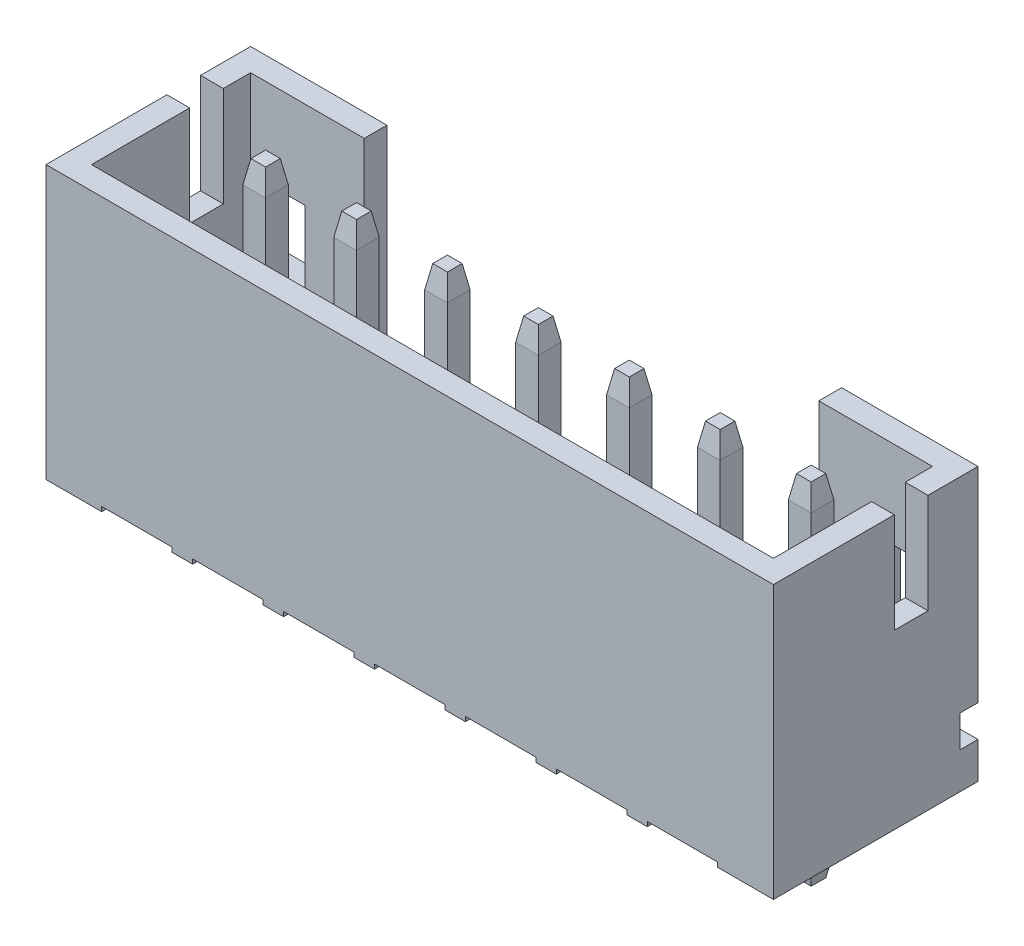
SolidWorks part; units mm, degrees
ref_plane "Front Plane" through (0, 0, 0) normal (0, 0, 1) x (1, 0, 0)
ref_plane "Top Plane" through (0, 0, 0) normal (0, 1, 0) x (1, 0, 0)
ref_plane "Right Plane" through (0, 0, 0) normal (1, 0, 0) x (0, 0, -1)
sketch "Sketch1" plane through (0, 0, 0) normal (0, 1, 0) x (1, 0, 0)
  line L1 (-10, 2.25) -> (6, 2.25)
  line L2 (-10, 2.25) -> (-10, -2.25)
  line L3 (-10, -2.25) -> (6, -2.25)
  line L4 (6, 2.25) -> (6, -2.25)
  dimension "D1" = 16
  dimension "D2" = 4.5
  dimension "D3" = 2.25
  dimension "D4" = 6
extrude "Extrude1" add sketch "Sketch1" along normal blind 6
sketch "Sketch2" plane through (0, 0, 2.25) normal (0, 0, 1) x (1, 0, 0)
  line L0 (-10, 0) -> (6, 0) construction
  line L6 (-0.775, 0.1) -> (0.775, 0.1)
  line L7 (-0.775, 0.1) -> (-0.775, 0)
  line L8 (-0.775, 0) -> (0, 0)
  line L9 (0.775, 0.1) -> (0.775, 0)
  line L10 (0, 0) -> (0.775, 0)
  dimension "D1" = 0.1
  dimension "D3" = 1.55
extrude "Cut-Extrude1" cut sketch "Sketch2" against normal through all
sketch "Sketch3" plane through (0, 6, 0) normal (0, 1, 0) x (-1, 0, 0)
  line L0 (-6, -2.25) -> (10, -2.25) construction
  line L1 (9.5, -1.75) -> (-5.5, -1.75)
  line L2 (9.5, -1.75) -> (9.5, 1.75)
  line L3 (9.5, 1.75) -> (-5.5, 1.75)
  line L4 (-5.5, -1.75) -> (-5.5, 1.75)
  line L5 (10, 2.25) -> (-6, 2.25) construction
  line L6 (-6, 2.25) -> (-6, -2.25) construction
  line L7 (10, -2.25) -> (10, 2.25) construction
  dimension "D1" = 0.5
  dimension "D2" = 0.5
  dimension "D3" = 0.5
  dimension "D4" = 0.5
extrude "Cut-Extrude2" cut sketch "Sketch3" against normal offset from surface (4.2 mm away) 1.8 up to face at (3.3875, 0, 0)
sketch "Sketch5" plane through (-10, 0, 0) normal (-1, 0, 0) x (0, 0, 1)
  line L1 (-1.15, 6) -> (-0.41, 6)
  line L2 (-1.15, 6) -> (-1.15, 3.8)
  line L3 (-1.15, 3.8) -> (-0.41, 3.8)
  line L4 (-0.41, 6) -> (-0.41, 3.8)
  line L5 (-2.25, 6) -> (-2.25, 0) construction
  line L6 (-2.25, 6) -> (2.25, 6) construction
  dimension "D1" = 2.2
  dimension "D2" = 0.74
  dimension "D3" = 1.1
extrude "Cut-Extrude3" cut sketch "Sketch5" against normal through all
sketch "Sketch6" plane through (0, 0, -2.25) normal (0, 0, -1) x (-1, 0, 0)
  line L1 (-6, 6) -> (10, 6) construction
  line L2 (-3, 6) -> (7, 6)
  line L3 (-3, 6) -> (-3, 2)
  line L4 (-3, 2) -> (7, 2)
  line L5 (7, 6) -> (7, 2)
  dimension "D1" = 10
  dimension "D2" = 3
  dimension "D3" = 4
extrude "Cut-Extrude4" cut sketch "Sketch6" against normal blind 1.2
ref_plane "Plane1" through (0, 8.5, 0) normal (0, 1, 0) x (-1, 0, 0)
sketch "Sketch8" plane through (0, 8.5, 0) normal (0, 1, 0) x (-1, 0, 0)
  line L0 (-6, 2.25) -> (-6, -2.25) construction
  line L1 (10, -2.25) -> (10, 2.25) construction
  line L2 (-6, 2.25) -> (-6, -2.25)
  line L3 (10, -2.25) -> (10, 2.25)
  line L4 (-6, 2.25) -> (10, 2.25)
  line L5 (10, -2.25) -> (-6, -2.25)
sketch "Sketch9" plane through (0, 0, 0) normal (1, 0, 0) x (0, 0, -1)
  line L0 (2.25, 6) -> (2.25, 0) construction
  line L1 (2.25, 1.5) -> (1.85, 1.5)
  line L2 (2.25, 1.5) -> (2.25, 0.8)
  line L3 (2.25, 0.8) -> (1.85, 0.8)
  line L4 (1.85, 1.5) -> (1.85, 0.8)
  line L5 (2.25, 0) -> (-2.25, 0) construction
  line L6 (-2.25, 6) -> (-2.25, 0) construction
  dimension "D1" = 0.8
  dimension "D2" = 0.7
  dimension "D3" = 4.1
extrude "Cut-Extrude5" cut sketch "Sketch9" against normal through all and the other way through all
sketch "Sketch10" plane through (0, 0, -2.25) normal (0, 0, -1) x (-1, 0, 0)
  line L0 (-5.5, 1.8) -> (-5.5, 6) construction
  line L1 (-5.5, 4.0716) -> (-4.3, 4.0716)
  line L2 (-5.5, 4.0716) -> (-5.5, 2.4716)
  line L3 (-5.5, 2.4716) -> (-4.3, 2.4716)
  line L4 (-4.3, 4.0716) -> (-4.3, 2.4716)
  line L5 (9.5, 1.8) -> (9.5, 6) construction
  line L6 (9.5, 4.0716) -> (8.3, 4.0716)
  line L7 (9.5, 4.0716) -> (9.5, 2.4716)
  line L8 (9.5, 2.4716) -> (8.3, 2.4716)
  line L9 (8.3, 4.0716) -> (8.3, 2.4716)
  dimension "D1" = 1.2
  dimension "D2" = 1.6
extrude "Cut-Extrude6" cut sketch "Sketch10" against normal up to surface (0.5 mm away) up to face at (-2, 3.95, -1.75)
sketch "Sketch11" plane through (0, 0, 0) normal (1, 0, 0) x (0, 0, -1)
  line L0 (0, 1.8) -> (-0.5764, 1.2236)
  line L1 (-1.75, 1.8) -> (1.75, 1.8) construction
  line L2 (-0.5764, 1.2236) -> (-1.75, 1.2236)
  line L3 (-1.75, 1.2236) -> (-1.75, 1.8)
  line L4 (-1.75, 1.8) -> (0, 1.8)
extrude "Cut-Extrude7" cut sketch "Sketch11" against normal up to surface and the other way up to surface
pattern_linear "LPattern4" count 3 spacing 2 along (1, 0, 0) count 5 spacing 2 along (-1, 0, 0) of "Cut-Extrude1"
sketch "Sketch7" plane through (0, 0, 0) normal (0, 1, 0) x (1, 0, 0)
  line L0 (0, 0.33) -> (0.25, 0.33)
  line L1 (-0.25, 0.33) -> (0, 0.33)
  line L2 (-0.25, 0.33) -> (-0.25, 0.83)
  line L3 (-0.25, 0.83) -> (0.25, 0.83)
  line L4 (0.25, 0.33) -> (0.25, 0.83)
  line L5 (0.775, 2.25) -> (-0.775, 2.25) construction
  dimension "D1" = 0.5
  dimension "D2" = 0.5
  dimension "D3" = 1.42
extrude "Extrude2" add sketch "Sketch7" along normal offset from surface 0.3 and the other way blind 2 up to face at (-2, 6, 0.795)
pattern_linear "LPattern2" count 3 spacing 2 along (1, 0, 0) count 5 spacing 2 along (-1, 0, 0) of "Extrude2"
chamfer "Chamfer1" distance 0.5 angle 10 56 edges at (0, -2, -0.33) (0.25, -2, -0.58) (0, -2, -0.83) (-0.25, -2, -0.58) (0.25, 5.7, -0.58) (0, 5.7, -0.33) (-0.25, 5.7, -0.58) (0, 5.7, -0.83) (4.25, 5.7, -0.58) (4, 5.7, -0.83) (4, 5.7, -0.33) (3.75, 5.7, -0.58) (-3.75, 5.7, -0.58) (-4, 5.7, -0.83) (-4, 5.7, -0.33) (-4.25, 5.7, -0.58) (-1.75, 5.7, -0.58) (-2, 5.7, -0.83) (-2, 5.7, -0.33) (-2.25, 5.7, -0.58) (2.25, 5.7, -0.58) (2, 5.7, -0.83) (2, 5.7, -0.33) (1.75, 5.7, -0.58) (4, -2, -0.83) (4, -2, -0.33) (4.25, -2, -0.58) (3.75, -2, -0.58) (2, -2, -0.83) (2, -2, -0.33) (2.25, -2, -0.58) (1.75, -2, -0.58) (-2, -2, -0.83) (-2, -2, -0.33) (-1.75, -2, -0.58) (-2.25, -2, -0.58) (-4, -2, -0.83) (-4, -2, -0.33) (-3.75, -2, -0.58) (-4.25, -2, -0.58) (-6, -2, -0.83) (-6, -2, -0.33) (-5.75, -2, -0.58) (-6.25, -2, -0.58) (-5.75, 5.7, -0.58) (-6, 5.7, -0.83) (-6, 5.7, -0.33) (-6.25, 5.7, -0.58) (-8, -2, -0.83) (-8, -2, -0.33) (-7.75, -2, -0.58) (-8.25, -2, -0.58) (-7.75, 5.7, -0.58) (-8, 5.7, -0.83) (-8, 5.7, -0.33) (-8.25, 5.7, -0.58)
sketch "Component_Outline" plane through (0, 0, 0) normal (0, 1, 0) x (1, 0, 0)
  line L0 (-10, 2.25) -> (6, -2.25) construction
  line L1 (6, 2.25) -> (-10, 2.25)
  line L2 (6, 2.25) -> (6, -2.25)
  line L3 (6, -2.25) -> (-10, -2.25)
  line L4 (-10, 2.25) -> (-10, -2.25)
  point P6 (-2, 0)
